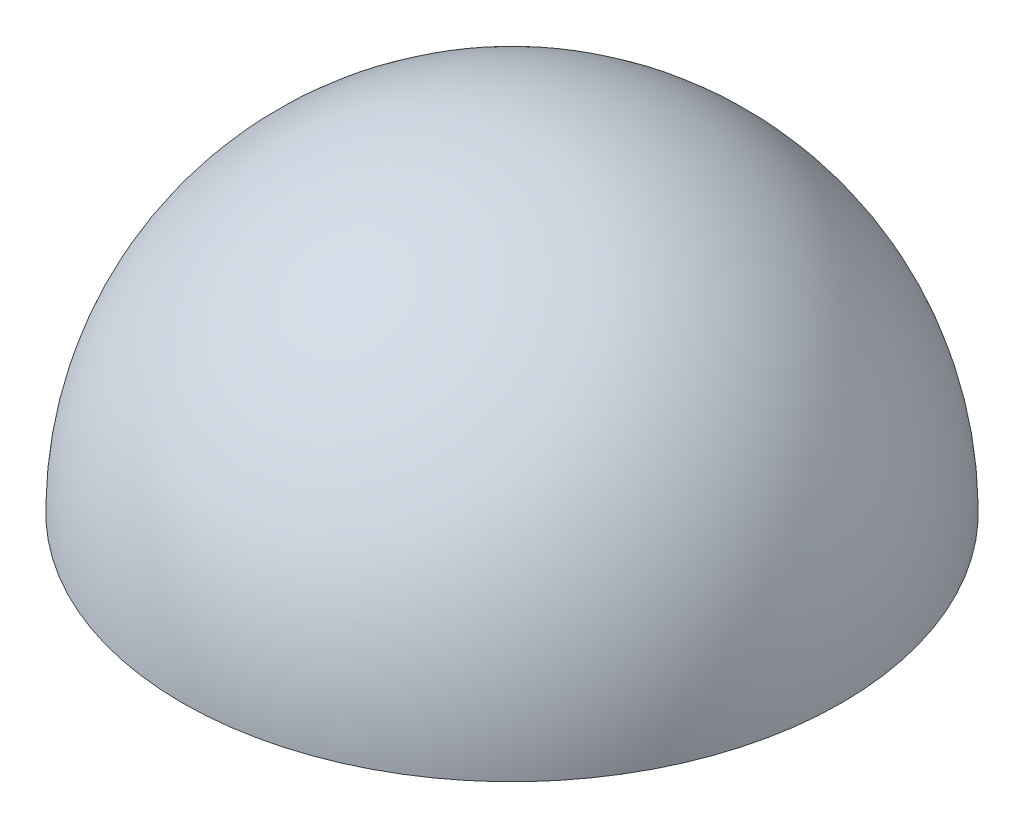
SolidWorks part; units mm, degrees
ref_plane "Front Plane" through (0, 0, 0) normal (0, 0, 1) x (1, 0, 0)
ref_plane "Top Plane" through (0, 0, 0) normal (0, 1, 0) x (1, 0, 0)
ref_plane "Right Plane" through (0, 0, 0) normal (1, 0, 0) x (0, 0, -1)
sketch "Sketch1" plane through (0, 0, 0) normal (0, 0, 1) x (1, 0, 0)
  line L0 (0, 1.5) -> (0, 0)
  line L1 (0, 0) -> (1.5, 0)
  arc A0 (0, 1.5) -> (1.5, 0) centre (0, 0) cw
  dimension "D1" = 1.5
revolve "Revolve1" add sketch "Sketch1" angle 360 about L0
